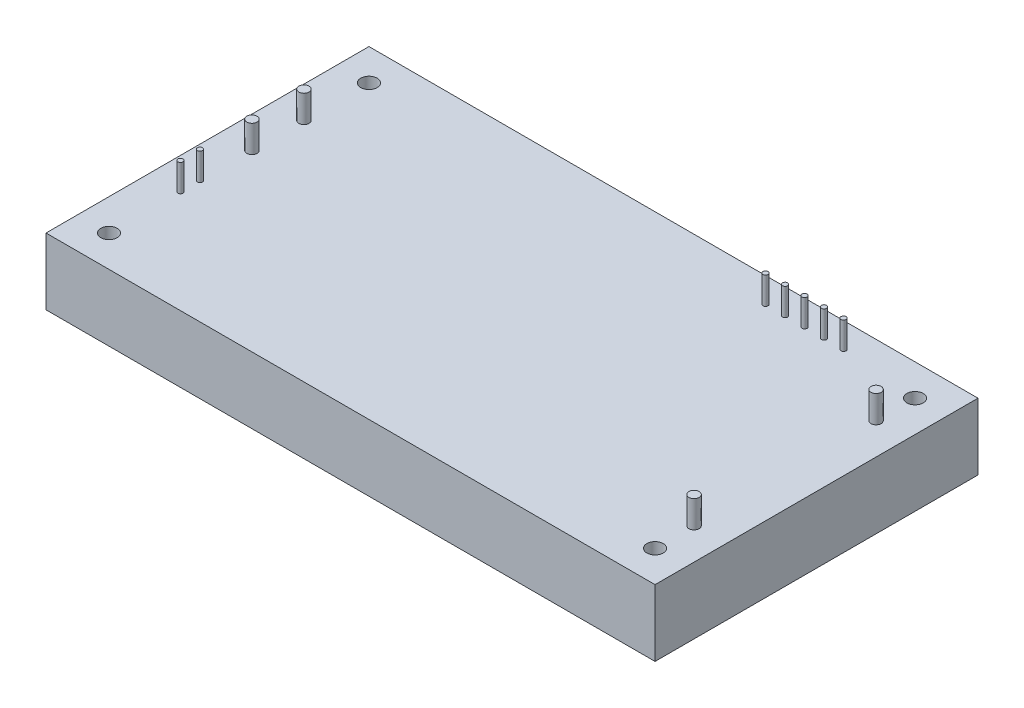
SolidWorks part; units mm, degrees
ref_plane "前视基准面" through (0, 0, 0) normal (0, 0, 1) x (1, 0, 0)
ref_plane "上视基准面" through (0, 0, 0) normal (0, 1, 0) x (1, 0, 0)
ref_plane "右视基准面" through (0, 0, 0) normal (1, 0, 0) x (0, 0, -1)
sketch "草图1" plane through (0, 0, 0) normal (0, 1, 0) x (1, 0, 0)
  line L1 (-59.5, -31.55) -> (59.5, -31.55)
  line L2 (-59.5, -31.55) -> (-59.5, 31.55)
  line L3 (-59.5, 31.55) -> (59.5, 31.55)
  line L4 (59.5, -31.55) -> (59.5, 31.55)
  line L5 (0, 31.55) -> (0, -31.55) construction
  line L6 (-59.5, 0) -> (59.5, 0) construction
  point P0 (0, 0)
  dimension "D1" = 119
  dimension "D2" = 63.1
extrude "凸台-拉伸1" add sketch "草图1" along normal blind 13
sketch "草图2" plane through (0, 13, 0) normal (0, 1, 0) x (1, 0, 0)
  circle A0 centre (53.35, 25.4) radius 1.6
  circle A1 centre (53.35, -25.4) radius 1.6
  circle A2 centre (-53.35, 25.4) radius 1.6
  circle A3 centre (-53.35, -25.4) radius 1.6
extrude "切除-拉伸2" cut sketch "草图2" against normal blind 13
sketch "草图3" plane through (0, 13, 0) normal (0, 1, 0) x (1, 0, 0)
  circle A0 centre (53.35, 17.78) radius 1
  circle A1 centre (53.35, -17.78) radius 1
  circle A2 centre (-53.35, 12.7) radius 1
  circle A3 centre (-53.35, 2.54) radius 1
  point P4 (53.35, 12.039)
  point P9 (0, 0)
extrude "凸台-拉伸2" add sketch "草图3" along normal blind 5.3
sketch "草图4" plane through (0, 13, 0) normal (0, 1, 0) x (1, 0, 0)
  circle A0 centre (-53.35, -7.62) radius 0.5
  circle A1 centre (-53.35, -11.43) radius 0.5
  circle A2 centre (34.3, 26.67) radius 0.5
  circle A3 centre (38.11, 26.67) radius 0.5
  circle A4 centre (30.49, 26.67) radius 0.5
  circle A5 centre (26.68, 26.67) radius 0.5
  circle A6 centre (22.87, 26.67) radius 0.5
  point P2 (0, 0)
  point P15 (0, 0)
extrude "凸台-拉伸3" add sketch "草图4" along normal blind 5.3
